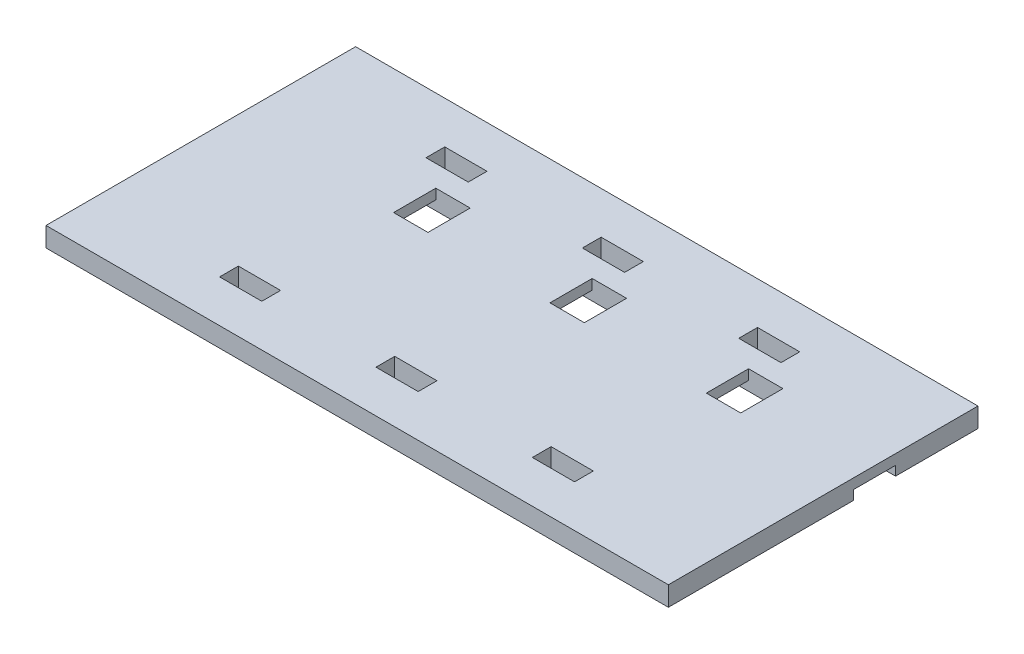
SolidWorks part; units mm, degrees
material "POLYURETHANE (11671)"
ref_plane "Front Plane" through (0, 0, 0) normal (0, 0, 1) x (1, 0, 0)
ref_plane "Top Plane" through (0, 0, 0) normal (0, 1, 0) x (1, 0, 0)
ref_plane "Right Plane" through (0, 0, 0) normal (1, 0, 0) x (0, 0, -1)
sketch "Sketch1" plane through (0, 0, 0) normal (0, 1, 0) x (1, 0, 0)
  line L1 (-50.546, -25.146) -> (50.546, -25.146)
  line L2 (-50.546, -25.146) -> (-50.546, 25.146)
  line L3 (-50.546, 25.146) -> (50.546, 25.146)
  line L4 (50.546, -25.146) -> (50.546, 25.146)
  line L5 (0, 25.146) -> (0, -25.146) construction
  line L6 (-50.546, 0) -> (50.546, 0) construction
  point P0 (0, 0)
  dimension "D1" = 50.292
  dimension "D2" = 101.092
extrude "Boss-Extrude1" add sketch "Sketch1" along normal blind 3.175
sketch "Sketch2" plane through (0, 3.175, 0) normal (0, 1, 0) x (1, 0, 0)
  line L0 (1.27, 4.8935) -> (6.858, 4.8935)
  line L1 (1.27, 4.8935) -> (1.27, 11.7515)
  line L2 (6.858, 4.8935) -> (6.858, 11.7515)
  line L3 (1.27, 11.7515) -> (6.858, 11.7515)
  circle A0 centre (4.064, 0) radius 5.635 construction
  dimension "D1" = 11.27
  dimension "D2" = 4.064
  dimension "D3" = 5.588
  dimension "D4" = 6.858
extrude "Wire Hole" cut sketch "Sketch2" against normal through all contours L3 L1 L0 L2
sketch "Sketch3" plane through (0, 3.175, 0) normal (0, 1, 0) x (1, 0, 0)
  line L0 (-3.81, 15.24) -> (3.048, 15.24)
  line L1 (-3.81, 15.24) -> (-3.81, 18.288)
  line L2 (3.048, 15.24) -> (3.048, 18.288)
  line L3 (-3.81, 18.288) -> (3.048, 18.288)
  line L4 (-3.4925, 0) -> (3.4925, 0) construction
  dimension "D1" = 3.048
  dimension "D2" = 6.858
  dimension "D3" = 3.048
  dimension "D4" = 15.24
extrude "Cut-Extrude2" cut sketch "Sketch3" against normal through all
mirror "Mirror1" about plane through (0, 0, 0) normal (0, 0, 1) of "Cut-Extrude2"
pattern_linear "LPattern1" count 2 spacing 25.4 along (-1, 0, 0) count 2 spacing 25.4 along (1, 0, 0) of "Wire Hole", "Cut-Extrude2", "Mirror1"
sketch "Sketch4" plane through (0, 0, 0) normal (0, 1, 0) x (1, 0, 0)
  line L0 (-50.546, 25.146) -> (-50.546, -25.146) construction
  line L1 (-50.546, 11.7515) -> (50.546, 11.7515)
  line L2 (-50.546, 11.7515) -> (-50.546, 4.8935)
  line L3 (-50.546, 4.8935) -> (50.546, 4.8935)
  line L4 (50.546, 11.7515) -> (50.546, 4.8935)
  line L5 (50.546, -25.146) -> (50.546, 25.146) construction
  line L7 (1.27, 11.7515) -> (6.858, 11.7515) construction
  line L8 (1.27, 4.8935) -> (6.858, 4.8935) construction
extrude "Cut-Extrude3" cut sketch "Sketch4" along normal blind 1.524
equation "\"Arrow Height\"= 1in"
equation "\"Button Height\"= 2in"
equation "\"Button Width\"= 4in"
equation "\"Haptic Diameter\"= 10mm"
equation "\"Haptic Thickness\"= 2.7mm"
equation "\"D1@Sketch1\"=\"Button Height\"-\"Tolerance\""
equation "\"D2@Sketch1\"=\"Button Width\"-\"Tolerance\""
equation "\"Arrow Spacing\"= 1in"
equation "\"Arrow Width\"= 0.75in"
equation "\"Haptic Wire Angle\"= 63.43"
equation "\"Haptic Wire Width\"= .2in"
equation "\"Hatic Wire Height\"= .25in"
equation "\"D1@Sketch2\"=\"Haptic Diameter\"+.05"
equation "\"D3@Sketch2\"=\"Haptic Wire Width\"+.02"
equation "\"D4@Sketch2\"=\"Hatic Wire Height\"+.02"
equation "\"Tolerance\"= .02in"
